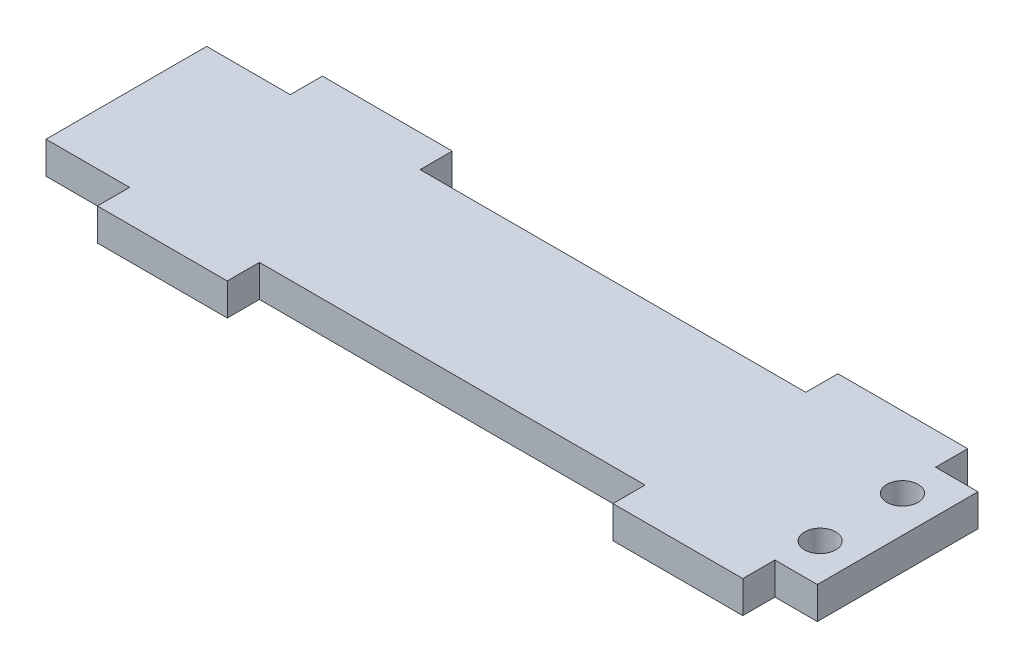
SolidWorks part; units mm, degrees
ref_plane "Front Plane" through (0, 0, 0) normal (0, 0, 1) x (1, 0, 0)
ref_plane "Top Plane" through (0, 0, 0) normal (0, 1, 0) x (1, 0, 0)
ref_plane "Right Plane" through (0, 0, 0) normal (1, 0, 0) x (0, 0, -1)
sketch "Sketch1" plane through (0, 0, 0) normal (0, 1, 0) x (1, 0, 0)
  line L0 (144.018, 0) -> (144.018, -6.35)
  line L1 (0, 31.75) -> (16.51, 31.75)
  line L2 (0, 31.75) -> (0, 0)
  line L3 (152.4, 31.75) -> (152.4, 0)
  line L4 (0, 15.875) -> (152.4, 15.875) construction
  line L5 (42.164, 31.75) -> (118.364, 31.75)
  line L6 (144.018, 31.75) -> (152.4, 31.75)
  line L7 (16.51, 31.75) -> (16.51, 38.1)
  line L8 (16.51, 38.1) -> (42.164, 38.1)
  line L9 (42.164, 31.75) -> (42.164, 38.1)
  line L10 (118.364, -6.35) -> (144.018, -6.35)
  line L11 (118.364, 31.75) -> (118.364, 38.1)
  line L12 (118.364, 38.1) -> (144.018, 38.1)
  line L13 (144.018, 31.75) -> (144.018, 38.1)
  line L14 (118.364, 0) -> (118.364, -6.35)
  line L15 (42.164, 0) -> (42.164, -6.35)
  line L16 (16.51, -6.35) -> (42.164, -6.35)
  line L17 (16.51, 0) -> (16.51, -6.35)
  line L18 (144.018, 0) -> (152.4, 0)
  line L19 (42.164, 0) -> (118.364, 0)
  line L20 (0, 0) -> (16.51, 0)
  circle A0 centre (145.2215, 7.7444) radius 3.0861
  circle A1 centre (145.2215, 24.0056) radius 3.0861
  dimension "D1" = 6.1722
  dimension "D3" = 16.51
  dimension "D4" = 25.654
  dimension "D5" = 6.35
  dimension "D6" = 6.35
  dimension "D7" = 25.654
  dimension "D8" = 76.2
extrude "Boss-Extrude1" add sketch "Sketch1" along normal blind 6.35
